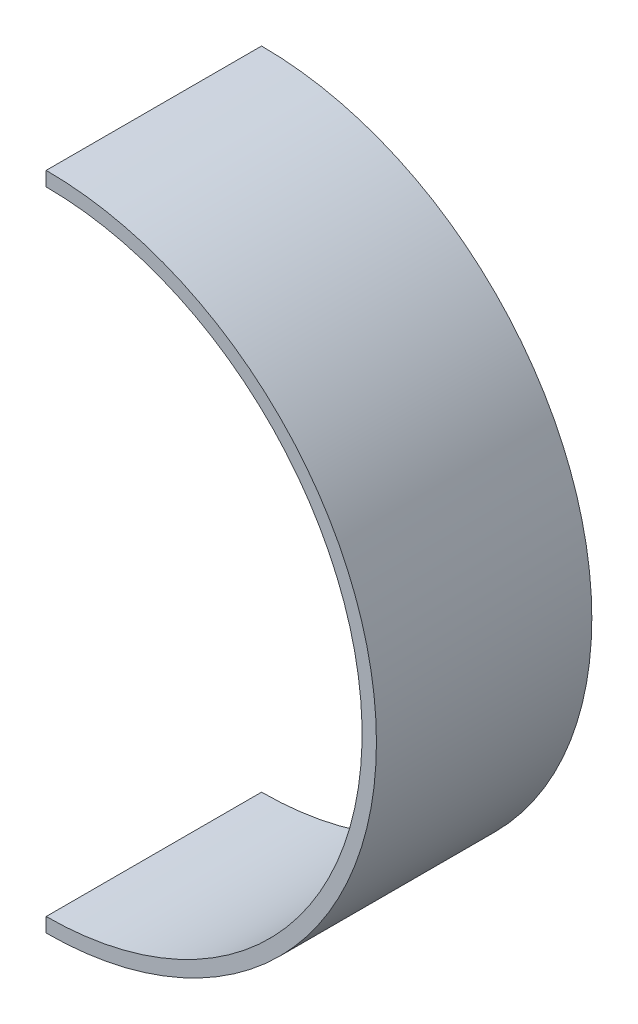
SolidWorks part; units mm, degrees
ref_plane "正面" through (0, 0, 0) normal (0, 0, 1) x (1, 0, 0)
ref_plane "平面" through (0, 0, 0) normal (0, 1, 0) x (1, 0, 0)
ref_plane "右側面" through (0, 0, 0) normal (1, 0, 0) x (0, 0, -1)
sketch "ｽｹｯﾁ1" plane through (0, 0, 0) normal (0, 0, 1) x (1, 0, 0)
  circle A0 centre (0, 0) radius 1
  dimension "D1" = 2
extrude "ﾎﾞｽ - 押し出し1" add sketch "ｽｹｯﾁ1" along normal blind 15
sketch "ｽｹｯﾁ2" plane through (0, 0, 15) normal (0, 0, 1) x (1, 0, 0)
  line L0 (0, -45) -> (0, 0) construction
  line L1 (0, -44.5) -> (0, -45.5)
  line L2 (0, 0.5) -> (0, -0.5)
  arc A0 (0, 0) -> (0, -45) centre (0, -22.5) cw construction
  arc A1 (0, -0.5) -> (0, -44.5) centre (0, -22.5) cw
  arc A2 (0, 0.5) -> (0, -45.5) centre (0, -22.5) cw
  dimension "D2" = 22.5
  dimension "D3" = 1
  dimension "D4" = 0.5
  dimension "D1" = 45
extrude "ﾎﾞｽ - 押し出し2" add sketch "ｽｹｯﾁ2" against normal blind 15
sketch "ｽｹｯﾁ5" plane through (0, 0, 0) normal (0, 0, -1) x (-1, 0, 0)
  point P0 (0, 0)
sketch3d "3Dｽｹｯﾁ1"
  line L0 (0, 0, 0) -> (-10, 0, 0)
  line L1 (0, 0, 0) -> (0, -10, 0)
  line L2 (0, 0, 0) -> (0, 0, 10)
  dimension "D1" = 10
  dimension "D2" = 10
  dimension "D3" = 10
sketch "ｽｹｯﾁ6" plane through (0, 0, 15) normal (0, 0, 1) x (1, 0, 0)
  line L0 (0, 0.5) -> (0, -0.5)
  line L1 (0.8562, -0.5167) -> (0.8562, -1.6844)
  line L2 (0, 0) -> (0, -10) construction
  line L3 (0.8562, -1.6844) -> (-3.3516, -1.6844)
  line L4 (-3.3516, -1.6844) -> (-3.3516, 1.7305)
  line L5 (-3.3516, 1.7305) -> (0.8754, 1.7305)
  line L6 (0.8754, 1.7305) -> (0.8754, 0.4833)
  arc A0 (0.8562, -0.5167) -> (0, -0.5) centre (0, -22.5) ccw
  arc A1 (0.8754, 0.4833) -> (0, 0.5) centre (0, -22.5) ccw
  point P5 (0, 0)
extrude "ｶｯﾄ - 押し出し1" cut sketch "ｽｹｯﾁ6" against normal through all
